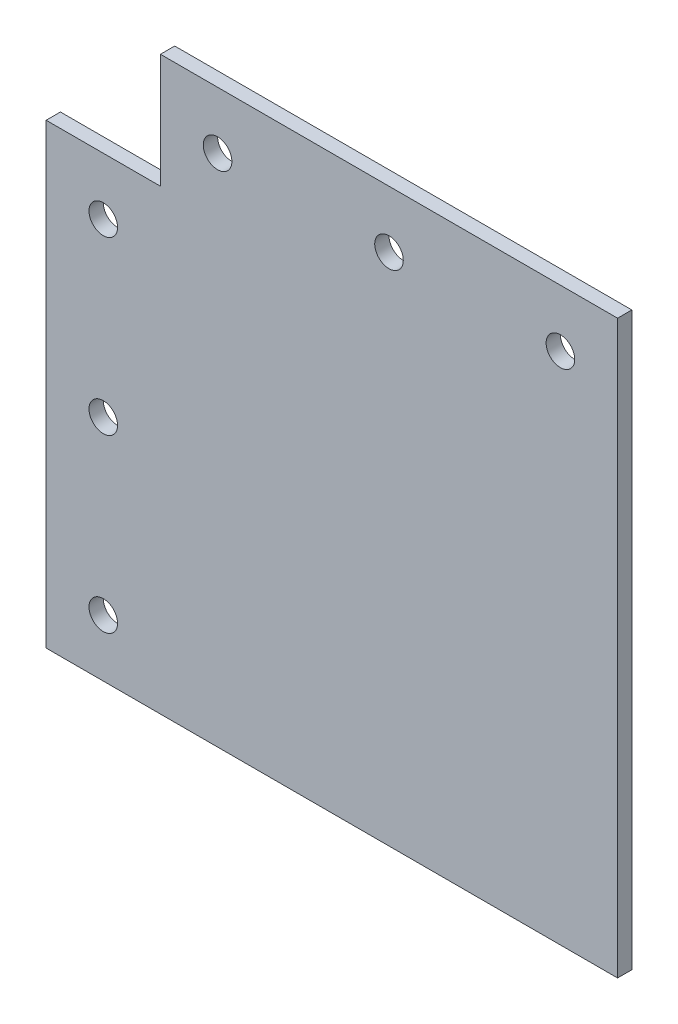
SolidWorks part; units mm, degrees
ref_plane "Front Plane" through (0, 0, 0) normal (0, 0, 1) x (1, 0, 0)
ref_plane "Top Plane" through (0, 0, 0) normal (0, 1, 0) x (1, 0, 0)
ref_plane "Right Plane" through (0, 0, 0) normal (1, 0, 0) x (0, 0, -1)
sketch "Sketch1" plane through (0, 0, 0) normal (0, 0, 1) x (1, 0, 0)
  line L0 (12.7, 101.6) -> (12.7, 0) construction
  line L1 (0, 0) -> (127, 0)
  line L2 (0, 0) -> (0, 101.6)
  line L3 (25.4, 127) -> (127, 127)
  line L4 (127, 0) -> (127, 127)
  line L5 (25.4, 114.3) -> (127, 114.3) construction
  line L6 (25.4, 127) -> (25.4, 101.6)
  line L7 (25.4, 101.6) -> (0, 101.6)
  circle A0 centre (12.7, 88.9) radius 3.175
  circle A1 centre (12.7, 50.8) radius 3.175
  circle A2 centre (12.7, 12.7) radius 3.175
  circle A3 centre (38.1, 114.3) radius 3.175
  circle A4 centre (76.2, 114.3) radius 3.175
  circle A5 centre (114.3, 114.3) radius 3.175
  dimension "D4" = 6.35
  dimension "D1" = 25.4
  dimension "D2" = 127
  dimension "D3" = 127
  dimension "D5" = 12.7
  dimension "D6" = 12.7
  dimension "D7" = 50.8
  dimension "D8" = 12.7
  dimension "D9" = 12.7
  dimension "D10" = 50.8
extrude "Boss-Extrude1" add sketch "Sketch1" along normal blind 3.175
